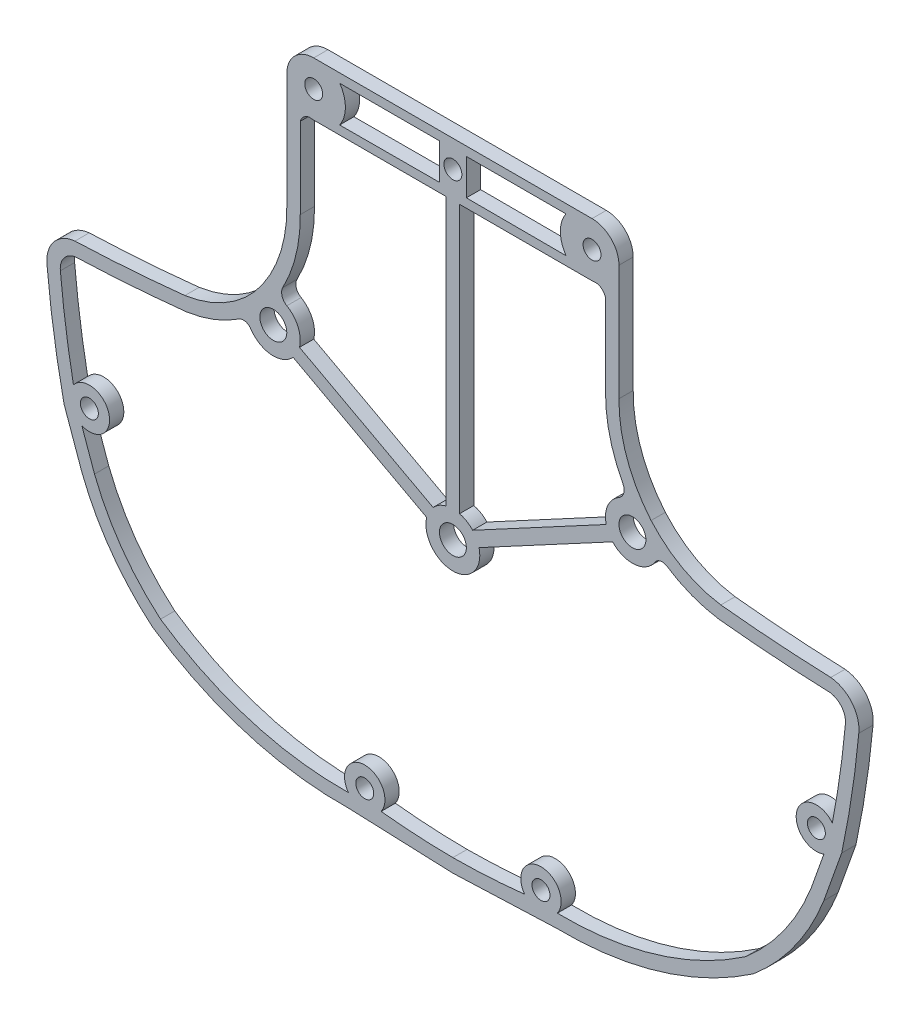
SolidWorks part; units mm, degrees
ref_plane "Front Plane" through (0, 0, 0) normal (0, 0, 1) x (1, 0, 0)
ref_plane "Top Plane" through (0, 0, 0) normal (0, 1, 0) x (1, 0, 0)
ref_plane "Right Plane" through (0, 0, 0) normal (1, 0, 0) x (0, 0, -1)
sketch "Sketch4" plane through (0, 0, 0) normal (0, 0, 1) x (1, 0, 0)
  line L0 (0, -3) -> (0, 1.5) construction
  line L1 (-41.3263, -9.6459) -> (-39.9169, -13.6055)
  line L2 (-11.6104, -31.6846) -> (0, -32.1446)
  line L3 (-15.5, 38.75) -> (15.5, 38.75)
  line L4 (-18.5, 35.75) -> (-18.5, 22.8725)
  line L5 (-17, 22.8813) -> (-17, 31.8851)
  line L6 (-43.3103, -8.5451) -> (-41.3154, -14.148)
  line L7 (43.3103, -8.5451) -> (41.3154, -14.148)
  line L8 (-15.5, 32.75) -> (-0.75, 32.75)
  line L9 (-41.3263, -9.6459) -> (-39.9169, -13.6055)
  line L10 (1.5, 37.75) -> (1.5, 33.75)
  line L11 (17, 22.8813) -> (17, 31.8851)
  line L12 (18.5, 35.75) -> (18.5, 22.8725)
  line L13 (11.6104, -31.6846) -> (0, -32.1446)
  line L14 (0, -32.1446) -> (0, -30.6446) construction
  line L15 (41.3263, -9.6459) -> (39.9169, -13.6055)
  line L17 (1.5, 33.75) -> (12.6125, 33.7217)
  line L18 (-1.5, 37.75) -> (-12.5929, 37.75)
  line L19 (-1.5, 33.75) -> (-12.6125, 33.7217)
  line L20 (-1.5, 37.75) -> (-1.5, 33.75)
  line L22 (1.5, 37.75) -> (12.5929, 37.75)
  line L23 (2.9136, 0.7146) -> (17.7965, 8.7142)
  line L25 (2.2035, 2.0358) -> (17.0864, 10.0354)
  line L26 (-2.2035, 2.0358) -> (-17.0864, 10.0354)
  line L27 (-43.3103, -8.5451) -> (-41.3154, -14.148)
  line L28 (-2.9136, 0.7146) -> (-17.7965, 8.7142)
  line L29 (-0.75, 32.75) -> (-0.75, 2.9047)
  line L30 (0.75, 32.75) -> (0.75, 2.9047)
  line L33 (0.75, 32.75) -> (15.5, 32.75)
  circle A0 centre (-16.9277, -13.0525) radius 0.75 construction
  circle A1 centre (0, -17.4912) radius 1.5 construction
  circle A2 centre (-20, 10.75) radius 1.5
  arc A3 (18.953, 14.8653) -> (17, 22.8813) centre (33.6375, 22.6888) cw
  circle A4 centre (-15.5, 35.75) radius 1
  arc A5 (-41.3154, -14.148) -> (-33.4728, -25.1215) centre (-15.9458, -4.3058) ccw
  arc A6 (-41.3263, -9.6459) -> (-42.2626, -6.1729) centre (-40.489, -7.5575) ccw
  arc A7 (-0.75, 2.9047) -> (-2.2035, 2.0358) centre (0, 0) ccw
  circle A8 centre (-9.8152, -28.8663) radius 1
  arc A9 (-39.9169, -13.6055) -> (-32.5625, -23.9268) centre (-15.9458, -4.3058) ccw
  arc A10 (-7.992, -30.1848) -> (-11.6383, -30.1848) centre (-9.8152, -28.8663) ccw
  arc A11 (-11.6383, -30.1848) -> (-32.5625, -23.9268) centre (-12.3075, 5.6876) cw
  arc A12 (15.5, 32.75) -> (15.955, 32.7847) centre (15.5, 35.75) ccw
  arc A13 (-15.955, 32.7847) -> (-15.5, 32.75) centre (-15.5, 35.75) ccw
  circle A14 centre (0, 0) radius 1.5
  arc A15 (-2.9136, 0.7146) -> (2.9136, 0.7146) centre (0, 0) ccw
  arc A16 (-11.6104, -31.6846) -> (-33.4728, -25.1215) centre (-12.3075, 5.6876) cw
  arc A17 (-11.5539, -27.4383) -> (-7.7996, -29.8663) centre (-9.8152, -28.8663) ccw construction
  arc A18 (39.9169, -13.6055) -> (32.5625, -23.9268) centre (15.9458, -4.3058) cw
  circle A19 centre (0, 35.75) radius 1
  arc A20 (-22.5154, 9.1152) -> (-17.7965, 8.7142) centre (-20, 10.75) ccw
  arc A21 (17, 31.8851) -> (15.955, 32.7847) centre (15.8188, 31.5698) ccw
  arc A22 (-43.3103, -8.5451) -> (-45.2127, 3.9531) centre (59.9942, 13.5734) cw
  arc A23 (-43.7203, 4.1043) -> (-41.989, 6.285) centre (-41.7643, 4.329) cw
  arc A24 (-7.992, -30.1848) -> (0, -30.6446) centre (0.4684, 47.1878) ccw
  arc A25 (-15.5, 38.75) -> (-18.5, 35.75) centre (-15.5, 35.75) ccw
  arc A26 (-18.953, 14.8653) -> (-18.4928, 13.3439) centre (-17.9197, 14.3475) ccw
  circle A27 centre (40.489, -7.5575) radius 1
  arc A28 (29.658, 7.1648) -> (23.8472, 9.3846) centre (31.7248, 21.2913) cw
  arc A29 (41.989, 6.285) -> (29.658, 7.1648) centre (48.4717, 183.9785) cw
  arc A30 (43.7203, 4.1043) -> (41.989, 6.285) centre (41.7643, 4.329) ccw
  arc A31 (42.2626, -6.1729) -> (43.7203, 4.1043) centre (-59.9942, 13.5734) ccw
  arc A32 (7.992, -30.1848) -> (0, -30.6446) centre (-0.4684, 47.1878) cw
  arc A33 (22.0771, 12.9146) -> (18.5, 22.8725) centre (33.6375, 22.6888) cw
  arc A34 (23.8472, 9.3846) -> (22.5154, 9.1151) centre (23.316, 8.584) ccw
  arc A35 (18.5, 35.75) -> (15.5, 38.75) centre (15.5, 35.75) ccw
  arc A36 (-45.2127, 3.9531) -> (-42.0937, 7.7821) centre (-41.7643, 4.329) cw
  circle A37 centre (-40.489, -7.5575) radius 1
  arc A38 (29.8468, 8.6532) -> (22.0771, 12.9146) centre (31.7248, 21.2913) cw
  arc A39 (42.0937, 7.7821) -> (29.8468, 8.6532) centre (48.4717, 183.9785) cw
  arc A40 (45.2127, 3.9531) -> (42.0937, 7.7821) centre (41.7643, 4.329) ccw
  arc A41 (11.6104, -31.6846) -> (33.4728, -25.1215) centre (12.3075, 5.6876) ccw
  arc A42 (42.2626, -6.1729) -> (41.3263, -9.6459) centre (40.489, -7.5575) ccw
  arc A43 (-42.0937, 7.7821) -> (-29.8468, 8.6532) centre (-48.4717, 183.9785) ccw
  arc A44 (-29.8468, 8.6532) -> (-22.0771, 12.9146) centre (-31.7248, 21.2913) ccw
  arc A45 (-43.3103, -8.5451) -> (-45.2127, 3.9531) centre (59.9942, 13.5734) cw
  arc A46 (-23.8472, 9.3846) -> (-22.5154, 9.1152) centre (-23.316, 8.584) cw
  arc A47 (-22.0771, 12.9146) -> (-18.5, 22.8725) centre (-33.6375, 22.6888) ccw
  arc A48 (11.6383, -30.1848) -> (32.5625, -23.9268) centre (12.3075, 5.6876) ccw
  arc A49 (-42.2626, -6.1729) -> (-43.7203, 4.1043) centre (59.9942, 13.5734) cw
  arc A50 (7.992, -30.1848) -> (11.6383, -30.1848) centre (9.8152, -28.8663) cw
  arc A51 (-41.989, 6.285) -> (-29.658, 7.1648) centre (-48.4717, 183.9785) ccw
  arc A52 (-29.658, 7.1648) -> (-23.8472, 9.3846) centre (-31.7248, 21.2913) ccw
  circle A53 centre (9.8152, -28.8663) radius 1
  arc A54 (41.3154, -14.148) -> (33.4728, -25.1215) centre (15.9458, -4.3058) cw
  arc A55 (-17, 31.8851) -> (-15.955, 32.7847) centre (-15.8188, 31.5698) cw
  arc A57 (-17.0864, 10.0354) -> (-18.5037, 13.3502) centre (-20, 10.75) ccw
  arc A58 (18.953, 14.8653) -> (18.4928, 13.3439) centre (17.9197, 14.3475) cw
  arc A65 (43.3103, -8.5451) -> (45.2127, 3.9531) centre (-59.9942, 13.5734) ccw
  arc A66 (22.5154, 9.1151) -> (17.7965, 8.7142) centre (20, 10.75) cw
  circle A72 centre (15.5, 35.75) radius 1
  circle A73 centre (20, 10.75) radius 1.5
  arc A74 (-18.953, 14.8653) -> (-17, 22.8813) centre (-33.6375, 22.6888) ccw
  arc A75 (-12.5929, 37.75) -> (-12.6125, 33.7217) centre (-15.5, 35.75) cw
  arc A77 (12.5929, 37.75) -> (12.6125, 33.7217) centre (15.5, 35.75) ccw
  arc A78 (2.2035, 2.0358) -> (0.75, 2.9047) centre (0, 0) ccw
  arc A79 (17.0864, 10.0354) -> (18.5037, 13.3502) centre (20, 10.75) cw
  point P16 (0, -7.5575)
  point P44 (0, 8.1)
  point P114 (0, 37.9632)
  dimension "D1" = 11.3751
  dimension "D3" = 1.5
  dimension "D2" = 9.8152
extrude "Boss-Extrude2" add sketch "Sketch4" along normal blind 1.5875
